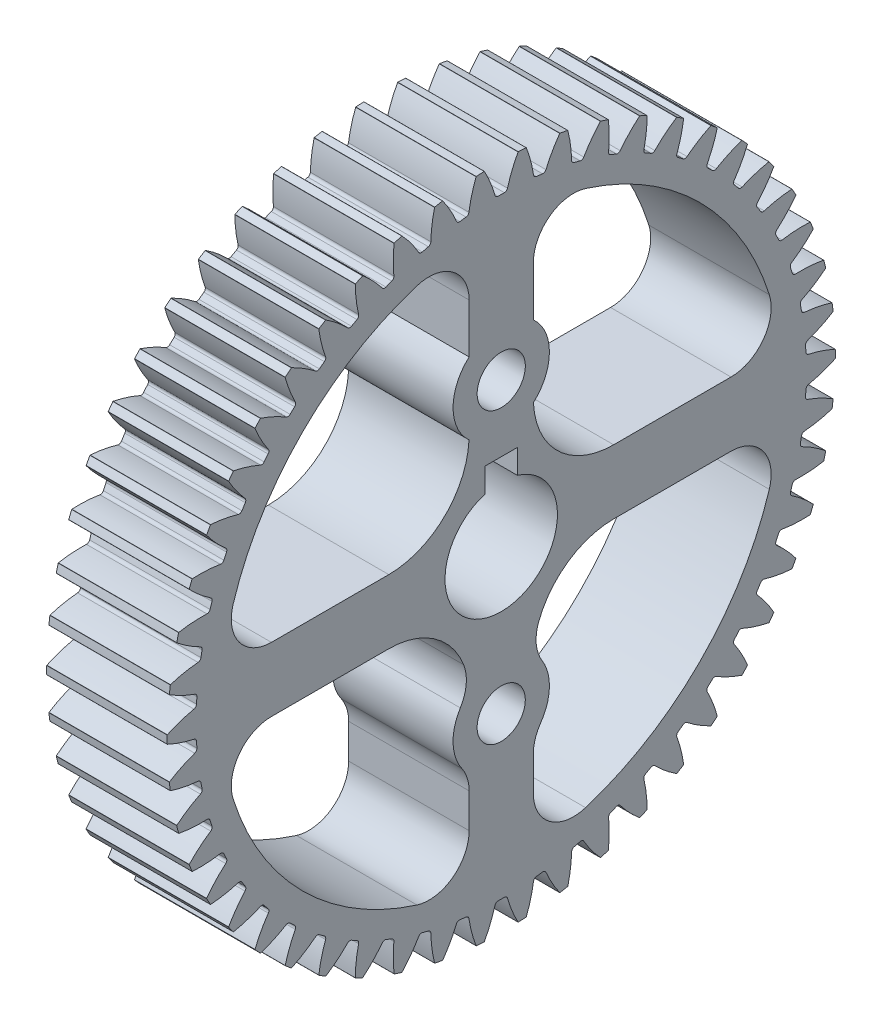
SolidWorks part; units mm, degrees
ref_plane "Plane1" through (0, 0, 0) normal (0, 0, 1) x (1, 0, 0)
ref_plane "Plane2" through (0, 0, 0) normal (0, 1, 0) x (1, 0, 0)
ref_plane "Plane3" through (0, 0, 0) normal (1, 0, 0) x (0, 0, -1)
other "Configuration Table"
sketch "HoldingSke" plane through (0, 0, 0) normal (0, 1, 0) x (1, 0, 0)
  line L0 (0, 0) -> (0.8035, -0.9576)
  line L1 (-15, 0) -> (100, 0) construction
  line L2 (0, 0) -> (-2.1039, 2.3779)
  line L3 (0, 0) -> (-11.863, 4.5341)
  line L4 (0, 0) -> (5.5511, 6.6156)
  line L5 (0, 0) -> (-46.8476, -17.4728)
  line L6 (0, 0) -> (-6.2172, -4.1948)
  line L7 (-2.1039, 2.3779) -> (8.6586, 51.2059)
  line L8 (-76.2, 54.61) -> (-76.1, 54.61)
  line L9 (-71.009, 38.7566) -> (-53.1078, 45.2721)
  line L10 (-76.2, 71.12) -> (104.1128, 71.12)
  line L11 (0, 0) -> (-7.5, 0)
  line L12 (-76.2, 101.6) -> (-76.17, 101.6)
  line L13 (24.9733, 27.94) -> (52.9518, 28.4284)
  line L14 (24.9733, 27.94) -> (24.9743, 27.94)
  line L15 (24.9733, 27.94) -> (100.4006, 29.5858)
  line L16 (-63.627, -0.8) -> (-12.827, -0.8)
  circle A0 centre (0, 0) radius 0.4
  circle A1 centre (0, 0) radius 18.999
  circle A2 centre (0, 0) radius 37.5
  circle A3 centre (0, 0) radius 0.4
  dimension "MHD" = 37.998
  dimension "Hub_dia" = 75
  dimension "Bore" = 0.8
  dimension "MBD" = 0.8
  dimension "Num_teeth" = 50
  dimension "Pitch" = 1.25
  dimension "Overall_len" = 50
  dimension "Show_teeth" = 50
  dimension "Thickness" = 7.5
  dimension "OAL" = 50.0001
  dimension "T_dim" = 0.1
  dimension "Ap" = 20
  dimension "H" = 19.05
  dimension "Pitch_radius" = 180.3128
  dimension "Width" = 7.5
  dimension "Backlash" = 0.03
  dimension "Addendum_fac" = 1
  dimension "Dedendum_fac" = 1.25
  dimension "Clearance_fac" = 0.25
  dimension "Dedendum_add" = 0.001
  dimension "Module" = 0.8
sketch "BasProSke" plane through (0, 0, 0) normal (0, 1, 0) x (1, 0, 0)
  line L0 (-10, 0) -> (60, 0) construction
  line L1 (0, 0) -> (0, 20.8)
  line L2 (0, 0) -> (7.5, 0)
  line L3 (7.5, 0) -> (7.5, 20.8)
  line L4 (7.5, 20.8) -> (0, 20.8)
  dimension "Thickness" = 7.5
  dimension "Diameter" = 41.6
revolve "Base-Revolve" add sketch "BasProSke" angle 360 about L0
sketch "TooCutSke" plane through (0, 0, 0) normal (1, 0, 0) x (0, 0, -1)
  line L1 (0, 0) -> (0, 107) construction
  line L2 (0, 0) -> (-0.6807, 19.9884) construction
  line L3 (0, 0) -> (-2.5106, 39.9045) construction
  line L4 (-0.6807, 19.9884) -> (-1.2553, 19.9523) construction
  arc A0 (0.3494, 18.9958) -> (-0.3494, 18.9958) centre (0, 0) ccw
  arc A1 (1.0655, 20.7981) -> (-1.0655, 20.7981) centre (0, 0) ccw
  circle A2 centre (0, 0) radius 20 construction
  circle A3 centre (0, 0) radius 18.7939 construction
  arc A4 (-0.3494, 18.9958) -> (-1.0655, 20.7981) centre (-8.0873, 16.9648) ccw
  arc A5 (1.0655, 20.7981) -> (0.3494, 18.9958) centre (8.0873, 16.9648) ccw
  dimension "Root_dia" = 37.998
  dimension "Overcut_dia" = 41.6508
  dimension "Pitch_dia" = 40
  dimension "Base_dia" = 37.5877
  dimension "Flank_rad" = 8
  dimension "Half_ang" = 3.6
  dimension "Half_CT" = 0.5757
extrude "ToothCut" cut sketch "TooCutSke" along normal through all
fillet "Breaks" radius 0.016 2 edges at (3.75, 20.7734, -1.0521) (3.75, 20.7734, 1.0521)
fillet "RootFillets" radius 0.201 2 edges at (3.75, 18.9958, -0.3494) (3.75, 18.9958, 0.3494)
pattern_circular "TeethCuts" count 50 every 7.2 about axis through (-10, 0, 0) along (1, 0, 0) of "ToothCut", "RootFillets", "Breaks"
sketch "HubNeaOneSke" plane through (0, 0, 0) normal (-1, 0, 0) x (0, 0, 1)
  circle A0 centre (0, 0) radius 18.999
  dimension "Diameter" = 37.998
extrude "HubNearOne" [suppressed] add sketch "HubNeaOneSke" along normal blind 42.5001
sketch "HubNeaBotSke" plane through (0, 0, 0) normal (-1, 0, 0) x (0, 0, 1)
  circle A0 centre (0, 0) radius 18.999
  dimension "Diameter" = 37.998
extrude "HubNearBoth" [suppressed] add sketch "HubNeaBotSke" along normal blind 21.25
ref_plane "FarPln" through (7.5, 0, 0) normal (1, 0, 0) x (0, 0, -1)
sketch "HubFarSke" plane through (7.5, 0, 0) normal (1, 0, 0) x (0, 0, -1)
  circle A0 centre (0, 0) radius 18.999
  dimension "Diameter" = 37.998
extrude "HubFar" [suppressed] add sketch "HubFarSke" along normal blind 21.25
sketch "BorSke" plane through (0, 0, 0) normal (1, 0, 0) x (0, 0, -1)
  circle A0 centre (0, 0) radius 0.4
  dimension "Diameter" = 0.8
extrude "Bore" cut sketch "BorSke" along normal mid plane 100.0001
sketch "KeySke" plane through (0, 0, 0) normal (1, 0, 0) x (0, 0, -1)
  line L0 (-0.05, 0) -> (-0.05, 0.5)
  line L1 (-0.05, 0.5) -> (0.05, 0.5)
  line L2 (0.05, 0.5) -> (0.05, 0)
  line L3 (0, 0) -> (0, 34) construction
  line L4 (-0.05, 0) -> (0.05, 0)
  dimension "Offset" = 0.5
  dimension "Width" = 0.1
extrude "Keyway" [suppressed] cut sketch "KeySke" along normal mid plane 100.0001
pattern_circular "Keyway2" [suppressed] count 2 every 90 about axis through (-10, 0, 0) along (1, 0, 0)
sketch "Sketch1" plane through (7.5, 0, 0) normal (1, 0, 0) x (0, 0, -1)
  circle A0 centre (0, 0) radius 0.4 construction
  circle A1 centre (0, 0) radius 0.4
extrude "Boss-Extrude1" add sketch "Sketch1" against normal up to surface (7.5 mm away) up to face at (0, 0, -0.4)
sketch "Sketch2" plane through (7.5, 0, 0) normal (1, 0, 0) x (0, 0, -1)
  line L0 (-13.0057, 13.8497) -> (-11.9789, 12.7562) construction
  circle A0 centre (0, 0) radius 17.499
  arc A1 (-12.8633, 13.9821) -> (-13.1468, 13.7158) centre (0, 0) ccw construction
  dimension "D1" = 1.5
extrude "Cut-Extrude1" cut sketch "Sketch2" against normal through all
sketch "Sketch3" plane through (7.5, 0, 0) normal (1, 0, 0) x (0, 0, -1)
  line L0 (17.499, 0) -> (-17.499, 0) construction
  line L1 (0, -17.499) -> (0, 17.499) construction
  line L2 (2, -17.3843) -> (2, -7)
  line L3 (-2, -17.3843) -> (-2, -7)
  line L4 (17.3843, 2) -> (7, 2)
  line L5 (17.3843, -2) -> (7, -2)
  line L6 (-2, 7) -> (-2, 17.3843)
  line L7 (-2, -17.499) -> (-2, 17.499) construction
  line L8 (-7, 2) -> (-17.3843, 2)
  line L9 (17.499, 2) -> (-17.499, 2) construction
  line L10 (2, 7) -> (2, 17.3843)
  line L11 (2, -17.499) -> (2, 17.499) construction
  line L12 (-7, -2) -> (-17.3843, -2)
  line L13 (17.499, -2) -> (-17.499, -2) construction
  circle A0 centre (0, 0) radius 17.499 construction
  arc A1 (-17.3843, 2) -> (-17.3843, -2) centre (0, 0) ccw
  arc A2 (-2, -17.3843) -> (2, -17.3843) centre (0, 0) ccw
  arc A3 (17.3843, -2) -> (17.3843, 2) centre (0, 0) ccw
  arc A4 (2, 17.3843) -> (-2, 17.3843) centre (0, 0) ccw
  arc A5 (-7, -2) -> (-2, -7) centre (-7, -7) cw
  arc A6 (2, -7) -> (7, -2) centre (7, -7) cw
  arc A7 (7, 2) -> (2, 7) centre (7, 7) cw
  arc A8 (-2, 7) -> (-7, 2) centre (-7, 7) cw
  point P6 (0, 0)
  point P9 (0, 0)
  point P34 (2, 2)
  point P37 (-2, 2)
  dimension "D5" = 5
  dimension "D1" = 2
  dimension "D2" = 2
  dimension "D3" = 2
  dimension "D4" = 2
extrude "Boss-Extrude2" add sketch "Sketch3" against normal up to surface (7.5 mm away) up to face at (0, 0, -17.499)
fillet "Fillet1" radius 2.5 8 edges at (3.75, -17.3843, 2) (3.75, -17.3843, -2) (3.75, -2, -17.3843) (3.75, 2, -17.3843) (3.75, 17.3843, -2) (3.75, -2, 17.3843) (3.75, 17.3843, 2) (3.75, 2, 17.3843)
sketch "Sketch4" plane through (7.5, 0, 0) normal (1, 0, 0) x (0, 0, -1)
  line L0 (0, 0) -> (0, 50000) construction
  line L1 (-1, 3.3541) -> (-1, 4.8541)
  line L2 (1, 3.3541) -> (1, 4.8541)
  line L3 (-1, 4.8541) -> (1, 4.8541)
  arc A0 (-1, 3.3541) -> (1, 3.3541) centre (0, 0) ccw
  dimension "D1" = 7
  dimension "D2" = 1.5
  dimension "D3" = 2
extrude "Cut-Extrude2" cut sketch "Sketch4" against normal through all
sketch "Sketch5" plane through (7.5, 0, 0) normal (1, 0, 0) x (0, 0, -1)
  line L0 (0, -9) -> (0, 0) construction
  line L1 (0, 0) -> (-50000, 0) construction
  circle A0 centre (0, -9) radius 3
  circle A1 centre (0, 9) radius 3
  dimension "D2" = 6
  dimension "D1" = 9
extrude "Boss-Extrude3" add sketch "Sketch5" against normal up to surface (7.5 mm away) up to face at (0, 2.3906, 0)
sketch "Sketch6" plane through (7.5, 0, 0) normal (1, 0, 0) x (0, 0, -1)
  line L0 (0, 0) -> (-50000, 0) construction
  circle A0 centre (0, 9) radius 1.5
  arc A1 (2, -11.2361) -> (2.0054, -6.7687) centre (0, -9) ccw construction
  circle A2 centre (0, -9) radius 1.5
  arc A4 (2, -11.2361) -> (2.0054, -6.7687) centre (0, -9) ccw construction
  dimension "D1" = 3
extrude "Cut-Extrude3" cut sketch "Sketch6" against normal through all
fillet "Fillet2" radius 2.5 4 edges at (3.75, -11.2361, 2) (3.75, -11.2361, -2) (3.75, -6.7687, -2.0054) (3.75, -6.7687, 2.0054)
equation "' \"Module@HoldingSke\" = 6.35"
equation "' \"Num_teeth@HoldingSke\" = 12"
equation "' \"Ap@HoldingSke\" =  20"
equation "' \"Ap@HoldingSke\" = 20"
equation "' \"Width@HoldingSke\" = 0.5 * 25.4"
equation "' \"Hub_dia@HoldingSke\"= 1 * 25.4"
equation "' \"Hub_dia@HoldingSke\" = 1 * 25.4"
equation "' \"Overall_len@HoldingSke\" = 1.0 * 25.4"
equation "' \"Bore@HoldingSke\" = 0.75 * 25.4"
equation "' \"T_dim@HoldingSke\" = 0.1 * 25.4"
equation "' \"Width@KeySke\" = 0.25 * 25.4"
equation "' \"Show_teeth@HoldingSke\" = 13"
equation "' \"Backlash@HoldingSke\" = 0.009 * 25.4"
equation "' \"Addendum_fac@HoldingSke\" = 1.0"
equation "' \"Dedendum_fac@HoldingSke\" = 1.25"
equation "' \"Dedendum_add@HoldingSke\" = 0.00005 * 25.4"
equation "' \"Clearance_fac@HoldingSke\" = 0.25"
equation "\"Pitch@HoldingSke\" = 1 / \"Module@HoldingSke\""
equation "\"Overcut_dia@TooCutSke\" = (\"Num_teeth@HoldingSke\" + 2 * \"Addendum_fac@HoldingSke\") / \"Pitch@HoldingSke\" + 0.002 * 25.4"
equation "\"Pitch_dia@TooCutSke\" = \"Num_teeth@HoldingSke\" / \"Pitch@HoldingSke\""
equation "\"Base_dia@TooCutSke\" = \"Num_teeth@HoldingSke\" / \"Pitch@HoldingSke\" * cos((\"Ap@HoldingSke\"  * 3.14159265 / 180))"
equation "\"Root_dia@TooCutSke\" = (\"Num_teeth@HoldingSke\" + 2) / \"Pitch@HoldingSke\" - 2 * (\"Addendum_fac@HoldingSke\" + \"Dedendum_fac@HoldingSke\") / \"Pitch@HoldingSke\" - \"Dedendum_add@HoldingSke\" * 2"
equation "\"Half_ang@TooCutSke\" = 180 / \"Num_teeth@HoldingSke\""
equation "\"Half_CT@TooCutSke\" = \"Num_teeth@HoldingSke\" / \"Pitch@HoldingSke\" * sin((3.14159265 / 2 / \"Num_teeth@HoldingSke\")) / 2 - 7 * \"Backlash@HoldingSke\" / 4"
equation "\"Flank_rad@TooCutSke\" = \"Num_teeth@HoldingSke\" / \"Pitch@HoldingSke\" / 5"
equation "\"Radius@RootFillets\" = \"Clearance_fac@HoldingSke\" / \"Pitch@HoldingSke\" + \"Dedendum_add@HoldingSke\""
equation "\"Break_rad@Breaks\" = 0.02 / \"Pitch@HoldingSke\""
equation "\"Thickness@HoldingSke\" = \"Width@HoldingSke\""
equation "\"OAL@HoldingSke\" = \"Thickness@HoldingSke\""
equation "\"MHD@HoldingSke\" = (\"Num_teeth@HoldingSke\" + 2) / \"Pitch@HoldingSke\" - 2 * (\"Addendum_fac@HoldingSke\" + \"Dedendum_fac@HoldingSke\")  / \"Pitch@HoldingSke\" - \"Dedendum_add@HoldingSke\" * 2"
equation "\"MBD@HoldingSke\" = (\"Num_teeth@HoldingSke\" + 2) / \"Pitch@HoldingSke\" - 2 * (\"Addendum_fac@HoldingSke\" + \"Dedendum_fac@HoldingSke\")  / \"Pitch@HoldingSke\" - \"Dedendum_add@HoldingSke\" * 2 - 0.002 * 25.4"
equation "\"MHD@HoldingSke\" = ((sgn( \"MHD@HoldingSke\" - \"Hub_dia@HoldingSke\" )-1)*( \"MHD@HoldingSke\" - \"Hub_dia@HoldingSke\" ))/-2+ \"Hub_dia@HoldingSke\""
equation "\"MBD@HoldingSke\" = ((sgn( \"MBD@HoldingSke\" - \"Bore@HoldingSke\" )-1)*( \"MBD@HoldingSke\" - \"Bore@HoldingSke\" ))/-2+ \"Bore@HoldingSke\""
equation "\"OAL@HoldingSke\" = ((sgn( \"OAL@HoldingSke\" - \"Overall_len@HoldingSke\" )+1)*( \"OAL@HoldingSke\" - \"Overall_len@HoldingSke\" ))/2 + \"Overall_len@HoldingSke\" + 0.000002 * 25.4"
equation "\"Num_teeth@TeethCuts\" = int( \"Show_teeth@HoldingSke\" ) + 1"
equation "\"Num_teeth@TeethCuts\" = ((sgn( \"Num_teeth@TeethCuts\" - \"Num_teeth@HoldingSke\" )-1)*( \"Num_teeth@TeethCuts\" - \"Num_teeth@HoldingSke\" ))/-2+ \"Num_teeth@HoldingSke\""
equation "\"Num_teeth@TeethCuts\" = ((sgn( \"Num_teeth@TeethCuts\" - 2.0)+1)*( \"Num_teeth@TeethCuts\" - 2.0))/2 +2.0"
equation "\"Angle@TeethCuts\" = 360.0 / \"Num_teeth@HoldingSke\""
equation "\"Diameter@BasProSke\" = (\"Num_teeth@HoldingSke\" + 2 * \"Addendum_fac@HoldingSke\") / \"Pitch@HoldingSke\""
equation "\"Thickness@BasProSke\"  = \"Thickness@HoldingSke\""
equation "' \"Fillet_rad@BasProSke\" =  \"Thickness@HoldingSke\" * 0.05"
equation "' \"Fillet_rad@BasProSke\" = \"Thickness@HoldingSke\" * 0.05"
equation "\"MHD@HoldingSke\" = ((sgn( \"MHD@HoldingSke\" - \"Root_dia@TooCutSke\" )-1)*( \"MHD@HoldingSke\" - \"Root_dia@TooCutSke\" ))/-2+ \"Root_dia@TooCutSke\""
equation "\"Diameter@HubNeaOneSke\" = \"MHD@HoldingSke\""
equation "\"Length@HubNearOne\" = \"OAL@HoldingSke\" - \"Thickness@BasProSke\""
equation "\"Diameter@HubNeaBotSke\" = \"MHD@HoldingSke\""
equation "\"Length@HubNearBoth\" = ( \"OAL@HoldingSke\" - \"Thickness@BasProSke\" ) / 2.0"
equation "\"Thickness@FarPln\" = \"Thickness@BasProSke\""
equation "\"Diameter@HubFarSke\" = \"MHD@HoldingSke\""
equation "\"Length@HubFar\" = ( \"OAL@HoldingSke\" - \"Thickness@BasProSke\" ) / 2.0"
equation "\"Diameter@BorSke\" = \"MBD@HoldingSke\""
equation "\"D1@Bore\" = \"OAL@HoldingSke\" * 2.0"
equation "\"D1@Keyway\" = \"OAL@HoldingSke\" * 2.0"
equation "\"Offset@KeySke\" = \"T_dim@HoldingSke\" + \"MBD@HoldingSke\" / 2.0"
